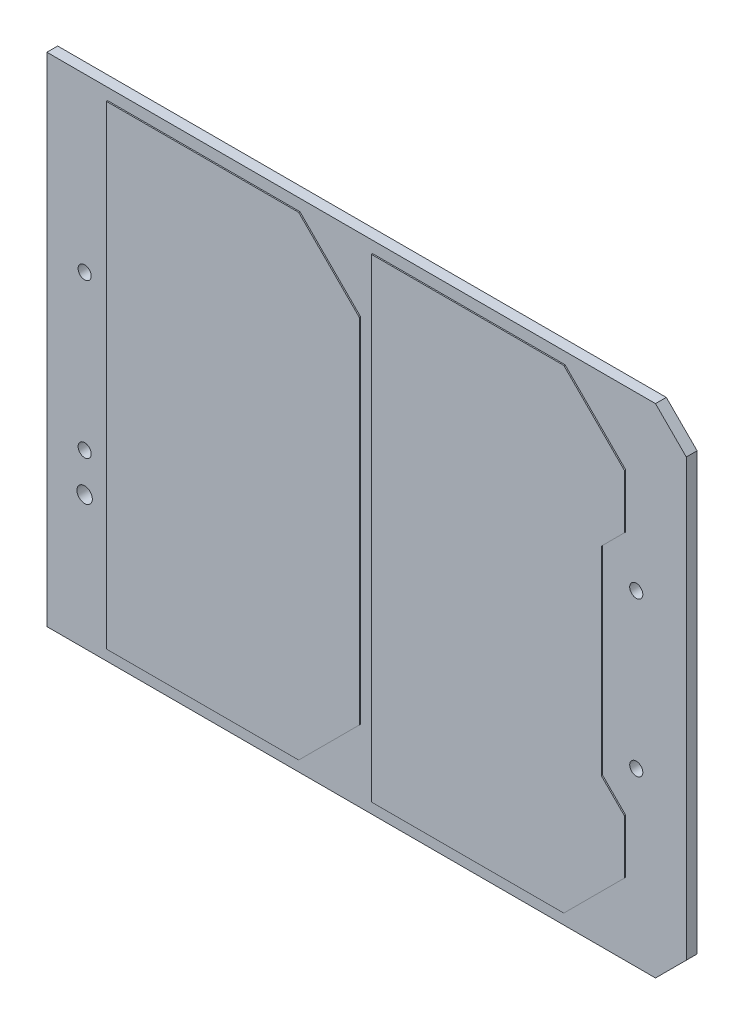
SolidWorks part; units mm, degrees
ref_plane "Front Plane" through (0, 0, 0) normal (0, 0, 1) x (1, 0, 0)
ref_plane "Top Plane" through (0, 0, 0) normal (0, 1, 0) x (1, 0, 0)
ref_plane "Right Plane" through (0, 0, 0) normal (1, 0, 0) x (0, 0, -1)
sketch "Sketch1" plane through (0, 0, 0) normal (0, 0, 1) x (1, 0, 0)
  line L0 (-46.482, 41) -> (-46.482, -41) construction
  line L1 (-52.705, -41) -> (52.705, -41)
  line L2 (-52.705, -41) -> (-52.705, 41)
  line L3 (-52.705, 41) -> (52.705, 41)
  line L4 (52.705, -41) -> (52.705, 41)
  line L5 (-52.705, -41) -> (52.705, 41) construction
  line L6 (-52.705, 41) -> (52.705, -41) construction
  line L7 (44.45, 41) -> (44.45, -41) construction
  circle A3 centre (44.45, 12.7) radius 1.0795
  circle A4 centre (44.45, -12.7) radius 1.0795
  circle A5 centre (-46.482, 12.7) radius 1.0795
  circle A6 centre (-46.482, -12.7) radius 1.0795
  circle A10 centre (-46.482, -19.05) radius 1.27
  point P0 (0, 0)
  dimension "D15" = 2.54
  dimension "D3" = 2.159
  dimension "D1" = 82
  dimension "D2" = 105.41
  dimension "D7" = 6.223
  dimension "D11" = 8.255
  dimension "D4" = 28.3
  dimension "D5" = 6.35
  dimension "D9" = 28.3
extrude "Boss-Extrude1" add sketch "Sketch1" along normal blind 1.778
sketch "Sketch2" plane through (0, 0, 1.778) normal (0, 0, 1) x (1, 0, 0)
  line L0 (-11, 39.095) -> (-1, 29.095)
  line L1 (-42.705, 39.095) -> (-11, 39.095)
  line L2 (-42.705, 39.095) -> (-42.705, -39.095)
  line L3 (-42.705, -39.095) -> (-11, -39.095)
  line L4 (-1, 29.095) -> (-1, -29.095)
  line L5 (-42.705, 39.095) -> (-1, -39.095) construction
  line L6 (-42.705, -39.095) -> (-1, 39.095) construction
  line L11 (42.705, 20.205) -> (38.895, 16.395)
  line L12 (38.895, 16.395) -> (38.895, -16.395)
  line L17 (38.895, -16.395) -> (42.705, -20.205)
  line L18 (-52.705, 41) -> (52.705, 41) construction
  line L23 (-52.705, -41) -> (52.705, -41) construction
  line L24 (42.705, -20.205) -> (42.705, -29.095)
  line L43 (1, 39.095) -> (32.705, 39.095)
  line L44 (1, 39.095) -> (1, -39.095)
  line L45 (1, -39.095) -> (32.705, -39.095)
  line L46 (42.705, 29.095) -> (42.705, 20.205)
  line L47 (1, 39.095) -> (42.705, -39.095) construction
  line L48 (1, -39.095) -> (42.705, 39.095) construction
  line L49 (-1, -29.095) -> (-11, -39.095)
  line L62 (32.705, -39.095) -> (42.705, -29.095)
  line L63 (32.705, 39.095) -> (42.705, 29.095)
  line L64 (-52.705, -41) -> (-52.705, 41) construction
  line L65 (52.705, -41) -> (52.705, 41) construction
  point P4 (-21.8525, 0)
  point P39 (21.8525, 0)
  point P76 (52.705, 0)
  dimension "D25" = 10
  dimension "D26" = 10
  dimension "D3" = 2
  dimension "D6" = 3.81
  dimension "D7" = 45
  dimension "D8" = 45
  dimension "D9" = 8.89
  dimension "D10" = 8.89
  dimension "D11" = 1.905
  dimension "D12" = 1.905
extrude "Boss-Extrude2" add sketch "Sketch2" along normal blind 0.2
sketch "Sketch3" plane through (0, 0, 1.978) normal (0, 0, 1) x (1, 0, 0)
  line L0 (-36.355, -32.745) -> (-36.355, 32.745)
  line L1 (-36.355, 32.745) -> (-13.6303, 32.745)
  line L2 (-13.6303, 32.745) -> (-7.35, 26.4647)
  line L3 (-7.35, 26.4647) -> (-7.35, -26.4647)
  line L4 (-7.35, -26.4647) -> (-13.6303, -32.745)
  line L5 (-13.6303, -32.745) -> (-36.355, -32.745)
  line L6 (7.35, -32.745) -> (7.35, 32.745)
  line L7 (7.35, 32.745) -> (30.0747, 32.745)
  line L8 (30.0747, 32.745) -> (36.355, 26.4647)
  line L9 (36.355, 26.4647) -> (36.355, -26.4647)
  line L10 (36.355, -26.4647) -> (30.0747, -32.745)
  line L11 (30.0747, -32.745) -> (7.35, -32.745)
  line L12 (-11, -39.095) -> (-1, -29.095) construction
  line L13 (-1, 29.095) -> (-11, 39.095) construction
  line L14 (-42.705, 39.095) -> (-42.705, -39.095) construction
  line L15 (-1, -29.095) -> (-1, 29.095) construction
  line L16 (-11, 39.095) -> (-42.705, 39.095) construction
  line L17 (-1, 29.095) -> (-11, 39.095) construction
  line L18 (-42.705, -39.095) -> (-11, -39.095) construction
  line L19 (1, 39.095) -> (1, -39.095) construction
  dimension "D5" = 6.35
  dimension "D1" = 6.35
  dimension "D2" = 6.35
  dimension "D3" = 6.35
  dimension "D4" = 6.35
  dimension "D6" = 6.35
extrude "Cut-Extrude1" [suppressed] cut sketch "Sketch3" against normal through all
chamfer "Chamfer1" [suppressed] distance 2.54 angle 45
chamfer "Chamfer2" distance 5.08 angle 45 2 edges at (52.705, -41, 0.889) (52.705, 41, 0.889)
equation "\"D26@Sketch2\"=\"D25@Sketch2\""
equation "\"D8@Sketch1\"=\"D6@Sketch1\""
equation "\"D4@Sketch1\"=(\"D1@Sketch1\"-\"D6@Sketch1\")/2"
equation "\"D9@Sketch1\"=\"D4@Sketch1\""
equation "\"D2@Sketch3\"=\"D1@Sketch3\""
equation "\"D3@Sketch3\"=\"D1@Sketch3\""
equation "\"D4@Sketch3\"=\"D3@Sketch3\""
equation "\"D5@Sketch3\"=\"D1@Sketch3\""
equation "\"D6@Sketch3\"=\"D1@Sketch3\""
equation "\"D10@Sketch2\"=\"D9@Sketch2\""
